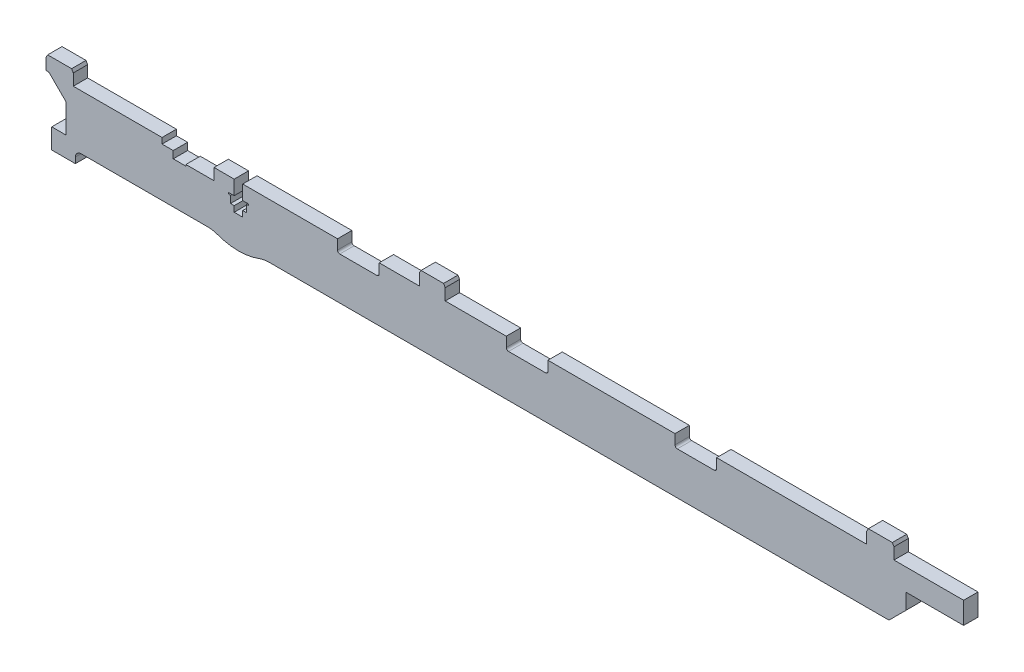
SolidWorks part; units mm, degrees
material "6061-T6 Black anodised"
ref_plane "Front Plane" through (0, 0, 0) normal (0, 0, 1) x (1, 0, 0)
ref_plane "Top Plane" through (0, 0, 0) normal (0, 1, 0) x (1, 0, 0)
ref_plane "Right Plane" through (0, 0, 0) normal (1, 0, 0) x (0, 0, -1)
sketch "Sketch1" plane through (0, 0, 0) normal (0, 0, 1) x (1, 0, 0)
  line L0 (-250.8, 3.6) -> (-241, 3.6)
  line L1 (0, 0) -> (20, 0)
  line L2 (-232.5, 8.6) -> (-232.5, -2.4) construction
  line L3 (-4.25, 7.6) -> (20, 7.6)
  line L4 (20, 0) -> (20, 7.6)
  line L5 (-13.75, 7.6) -> (-66, 7.6)
  line L6 (0, 0) -> (0, -11.4)
  line L7 (0, -11.4) -> (-221.7995, -11.4)
  line L8 (-292.5, 1.6) -> (-292.5, -8.4)
  line L9 (-259.0932, 7.6) -> (-290, 7.6)
  line L10 (-299.5, 7.6) -> (-299.5, 12.6)
  line L11 (-299.5, 12.6) -> (-290, 12.6)
  line L12 (-290, 7.6) -> (-290, 12.6)
  line L13 (-169.5, 7.6) -> (-169.5, 12.6)
  line L14 (-250.8, 3.6) -> (-250.8, 3.1)
  line L15 (-250.8, 3.1) -> (-255.2, 3.1)
  line L16 (-255.2, 3.1) -> (-255.2, 5.6)
  line L17 (-255.2, 5.6) -> (-259.0932, 5.6)
  line L18 (-4.25, 7.6) -> (-4.25, 12.6)
  line L19 (-4.25, 12.6) -> (-13.75, 12.6)
  line L20 (-13.75, 7.6) -> (-13.75, 12.6)
  line L21 (-259.0932, 5.6) -> (-259.0932, 7.6)
  line L22 (-255, 3.6) -> (-251, 3.6) construction
  line L23 (-255, 3.6) -> (-255, 13.6) construction
  line L24 (-251, 3.6) -> (-251, 13.6) construction
  line L25 (-255, 13.6) -> (-251, 13.6) construction
  line L26 (-255, 3.6) -> (-251, 13.6) construction
  line L27 (-271, 32.6) -> (-219.2068, 32.6) construction
  line L28 (-271, 32.6) -> (-271, 13.6) construction
  line L29 (-250, 33.6) -> (-250, 13.6) construction
  line L30 (-271, 13.6) -> (-250, 13.6) construction
  line L31 (-271, 32.6) -> (-250, 13.6) construction
  line L32 (-250, 33.6) -> (-271, 13.6) construction
  line L33 (-169.5, 12.6) -> (-160.5, 12.6)
  line L34 (-160.5, 12.6) -> (-160.5, 7.6)
  line L35 (-169.5, 7.6) -> (-183.5, 7.6)
  line L36 (-299.5, 7.6) -> (-298.5, 7.6)
  line L37 (-298.5, 7.6) -> (-292.5, 1.6)
  line L38 (-233.98, 7.6) -> (-233.98, 2.6)
  line L39 (-233.98, 2.6) -> (-236, 2.6)
  line L40 (-236, 2.6) -> (-236, 2.1)
  line L41 (-236, 2.1) -> (-235.25, 2.1)
  line L42 (-235.25, 2.1) -> (-235.25, -0.4)
  line L43 (-235.25, -0.4) -> (-233.98, -0.4)
  line L44 (-233.98, -0.4) -> (-233.98, -2.4)
  line L45 (-233.98, -2.4) -> (-231.02, -2.4)
  line L46 (-233.98, 7.6) -> (-241, 7.6)
  line L47 (-231.02, -0.4) -> (-231.02, -2.4)
  line L48 (-229.75, -0.4) -> (-231.02, -0.4)
  line L49 (-229.75, 2.1) -> (-229.75, -0.4)
  line L50 (-229, 2.1) -> (-229.75, 2.1)
  line L51 (-229, 2.6) -> (-229, 2.1)
  line L52 (-231.02, 2.6) -> (-229, 2.6)
  line L53 (-231.02, 7.6) -> (-231.02, 2.6)
  line L54 (-283, -20.0132) -> (-282, -18.2812)
  line L55 (-243.2005, -11.4) -> (-287.2708, -11.4)
  line L56 (-282, -15.4) -> (-287.2708, -15.4)
  line L57 (-251, 3.6) -> (-255, 13.6) construction
  line L58 (-282, -15.4) -> (-282, -18.2812)
  line L59 (-198, 7.6) -> (-231.02, 7.6)
  line L60 (-282, -30.9) -> (-297.5, -30.9)
  line L61 (-297.5, -30.9) -> (-297.5, -8.4)
  line L62 (-297.5, -8.4) -> (-292.5, -8.4)
  line L63 (-283, -25.7868) -> (-282, -27.5188)
  line L64 (-282, -23.9) -> (-282, -20.3633) construction
  line L65 (-283, -20.0132) -> (-286, -18.2812)
  line L66 (-286, -18.2812) -> (-290, -20.5906)
  line L67 (-290, -20.5906) -> (-290, -25.2094)
  line L68 (-290, -25.2094) -> (-286, -27.5188)
  line L69 (-286, -27.5188) -> (-283, -25.7868)
  line L70 (-282, -27.5188) -> (-282, -30.9)
  line L71 (-139.25, 7.6) -> (-160.5, 7.6)
  line L72 (-198, 7.6) -> (-198, 3.4)
  line L73 (-198, 3.4) -> (-183.5, 3.4)
  line L74 (-183.5, 7.6) -> (-183.5, 3.4)
  line L75 (-80.5, 7.6) -> (-124.75, 7.6)
  line L76 (-139.25, 7.6) -> (-139.25, 3.4)
  line L77 (-139.25, 3.4) -> (-124.75, 3.4)
  line L78 (-124.75, 7.6) -> (-124.75, 3.4)
  line L80 (-80.5, 7.6) -> (-80.5, 3.4)
  line L81 (-80.5, 3.4) -> (-66, 3.4)
  line L82 (-66, 7.6) -> (-66, 3.4)
  line L100 (-253, 8.6) -> (-238.8671, 8.6) construction
  line L116 (-241, 7.6) -> (-241, 3.6)
  arc A0 (-287.2708, -11.4) -> (-287.2708, -15.4) centre (-287.2708, -13.4) ccw
  circle A1 centre (-286, -22.9) radius 4 construction
  arc A2 (-221.7995, -11.4) -> (-225.2612, -12.0183) centre (-221.7995, -21.4) ccw
  arc A4 (-243.2005, -11.4) -> (-239.7388, -12.0183) centre (-243.2005, -21.4) cw
  arc A5 (-239.7388, -12.0183) -> (-225.2612, -12.0183) centre (-232.5, 7.6) ccw
  point P27 (-253, 8.6)
  point P130 (-242, 8.6)
  dimension "D34" = 8
  dimension "D35" = 2
  dimension "D39" = 10
  dimension "D2" = 20
  dimension "D3" = 7.6
  dimension "D4" = 5
  dimension "D5" = 11.4
  dimension "D7" = 9.5
  dimension "D8" = 6
  dimension "D18" = 20
  dimension "D19" = 42.5
  dimension "D20" = 25
  dimension "D14" = 10
  dimension "D15" = 4
  dimension "D45" = 1
  dimension "D6" = 1
  dimension "D10" = 6
  dimension "D21" = 0.5
  dimension "D22" = 0.2
  dimension "D23" = 0.2
  dimension "D11" = 4
  dimension "D12" = 9
  dimension "D13" = 189.5
  dimension "D9" = 6
  dimension "D16" = 1
  dimension "D17" = 8.5
  dimension "D24" = 0.5
  dimension "D25" = 2.5
  dimension "D26" = 2
  dimension "D27" = 2.96
  dimension "D28" = 11
  dimension "D29" = 7
  dimension "D30" = 5.5
  dimension "D31" = 270
  dimension "D32" = 11.5
  dimension "D33" = 6.5
  dimension "D36" = 5
  dimension "D37" = 8
  dimension "D38" = 16
  dimension "D40" = 9
  dimension "D41" = 13.75
  dimension "D42" = 14.5
  dimension "D43" = 58.75
  dimension "D44" = 58.75
  dimension "D46" = 52
  dimension "D47" = 4.2
extrude "Boss-Extrude1" add sketch "Sketch1" along normal blind 5
chamfer "Chamfer1" distance 6 angle 45 1 edges at (0, -11.4, 2.5)
chamfer "Chamfer2" [suppressed] distance 2.6 angle 60
sketch "Sketch2" plane through (-241, 0, 0) normal (-1, 0, 0) x (0, 0, 1)
  line L0 (5, 5.6) -> (2, 5.6) construction
  line L1 (5, 7.6) -> (5, 3.6) construction
  line L2 (2, 6.475) -> (2, 5.6) construction
  circle A0 centre (2, 5.6) radius 0.4645
extrude "Cut-Extrude1" [suppressed] cut sketch "Sketch2" against normal blind 0.5
sketch "Sketch3" plane through (0, 0, 5) normal (0, 0, 1) x (1, 0, 0)
  line L0 (-289.2708, -13.4) -> (-289.2708, -15.4)
  line L1 (-289.2708, -15.4) -> (-297.5, -15.4)
  line L2 (-282, -13.4) -> (-282, -30.9)
  line L3 (-282, -30.9) -> (-297.5, -30.9)
  line L4 (-297.5, -15.4) -> (-297.5, -30.9)
  line L5 (-289.2708, -13.4) -> (-282, -13.4)
  arc A0 (-287.2708, -11.4) -> (-287.2708, -15.4) centre (-287.2708, -13.4) ccw construction
extrude "Cut-Extrude2" cut sketch "Sketch3" against normal through all
chamfer "Chamfer3" distance 1 angle 30 3 edges at (-290, 12.6, 2.5) (-160.5, 12.6, 2.5) (-4.25, 12.6, 2.5)
chamfer "Chamfer4" distance 1 angle 30 3 edges at (-13.75, 12.6, 2.5) (-169.5, 12.6, 2.5) (-299.5, 12.6, 2.5)
fillet "Fillet1" radius 0.8 6 edges at (-66, 3.4, 2.5) (-80.5, 3.4, 2.5) (-124.75, 3.4, 2.5) (-139.25, 3.4, 2.5) (-183.5, 3.4, 2.5) (-198, 3.4, 2.5)
equation "\"y-plate-thickness\"=5"
equation "\"bed-plate-thickness\"=6"
equation "\"x-plate-thickness\"=5"
equation "\"rod-diameter\"=12"
equation "\"D4@Sketch1\"=\"x-plate-thickness\""
equation "\"D1@Boss-Extrude1\"=\"x-plate-thickness\""
equation "\"D44@Sketch1\"=\"D43@Sketch1\""
